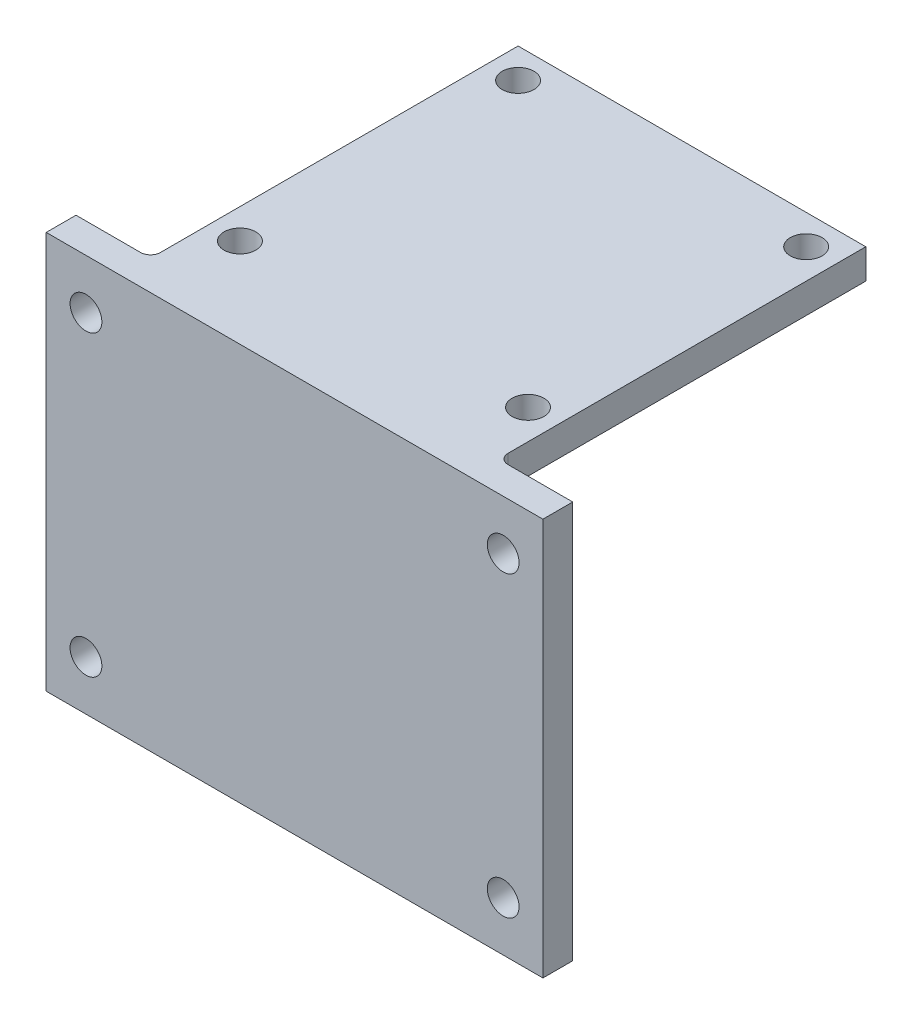
SolidWorks part; units mm, degrees
ref_plane "Front Plane" through (0, 0, 0) normal (0, 0, 1) x (1, 0, 0)
ref_plane "Top Plane" through (0, 0, 0) normal (0, 1, 0) x (1, 0, 0)
ref_plane "Right Plane" through (0, 0, 0) normal (1, 0, 0) x (0, 0, -1)
sketch "Sketch1" plane through (0, 0, 0) normal (0, 1, 0) x (1, 0, 0)
  line L0 (-14.9048, 13.5072) -> (20.0952, 13.5072)
  line L1 (-11.9048, 10.5072) -> (17.0952, 10.5072) construction
  line L2 (-11.9048, 10.5072) -> (-11.9048, -17.4928) construction
  line L3 (-11.9048, -17.4928) -> (17.0952, -17.4928) construction
  line L4 (17.0952, 10.5072) -> (17.0952, -17.4928) construction
  line L5 (20.0952, 13.5072) -> (20.0952, -23.4928)
  line L6 (-14.9048, -23.4928) -> (20.0952, -23.4928)
  line L7 (-14.9048, 13.5072) -> (-14.9048, -23.4928)
  circle A0 centre (-11.9048, 10.5072) radius 1.6
  circle A1 centre (-11.9048, -17.4928) radius 1.6
  circle A2 centre (17.0952, -17.4928) radius 1.6
  circle A3 centre (17.0952, 10.5072) radius 1.6
  dimension "D3" = 3.2
  dimension "D1" = 29
  dimension "D2" = 28
  dimension "D4" = 3
  dimension "D5" = 6
  dimension "D6" = 3
  dimension "D7" = 3
extrude "Boss-Extrude1" add sketch "Sketch1" along normal blind 3
sketch "Sketch2" plane through (0, 0, 23.4928) normal (0, 0, 1) x (1, 0, 0)
  line L0 (-14.9048, 0) -> (20.0952, 0) construction
  line L1 (27.5952, 3) -> (-22.4048, 3)
  line L2 (27.5952, 3) -> (27.5952, -37)
  line L3 (27.5952, -37) -> (-22.4048, -37)
  line L4 (-22.4048, 3) -> (-22.4048, -37)
  line L5 (2.5952, 3) -> (2.5952, -37) construction
  line L6 (-18.4048, -17) -> (23.5952, -17) construction
  line L7 (23.5952, -32) -> (-18.4048, -32) construction
  line L8 (23.5952, -32) -> (23.5952, -2) construction
  line L9 (23.5952, -2) -> (-18.4048, -2) construction
  line L10 (-18.4048, -32) -> (-18.4048, -2) construction
  circle A0 centre (23.5952, -32) radius 1.6
  circle A1 centre (23.5952, -2) radius 1.6
  circle A2 centre (-18.4048, -2) radius 1.6
  circle A3 centre (-18.4048, -32) radius 1.6
  point P6 (2.5952, 0)
  point P8 (2.5952, -2)
  point P17 (2.5952, -17)
  dimension "D5" = 3.2
  dimension "D1" = 40
  dimension "D2" = 50
  dimension "D3" = 30
  dimension "D4" = 42
extrude "Boss-Extrude2" add sketch "Sketch2" along normal blind 3
fillet "Fillet1" radius 3 1 edges at (2.5952, 0, 23.4928)
fillet "Fillet2" radius 1 1 edges at (-14.9048, 0, 23.4928)
fillet "Fillet3" radius 1 1 edges at (20.0952, 0, 23.4928)
